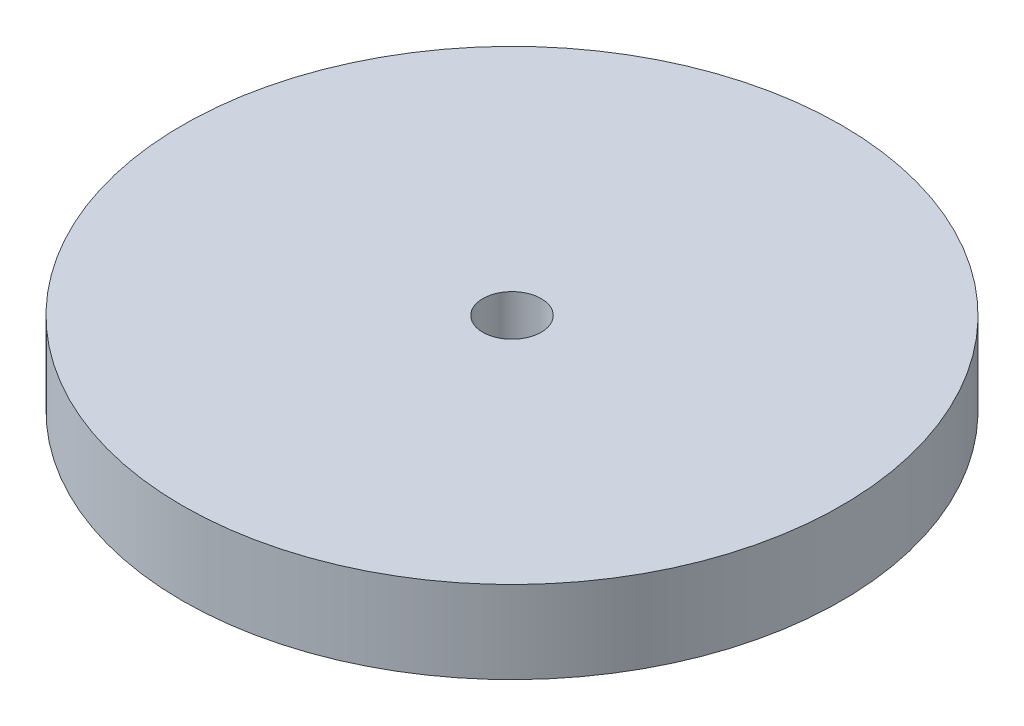
SolidWorks part; units mm, degrees
ref_plane "Front Plane" through (0, 0, 0) normal (0, 0, 1) x (1, 0, 0)
ref_plane "Top Plane" through (0, 0, 0) normal (0, 1, 0) x (1, 0, 0)
ref_plane "Right Plane" through (0, 0, 0) normal (1, 0, 0) x (0, 0, -1)
sketch "Sketch1" plane through (0, 0, 0) normal (0, 1, 0) x (1, 0, 0)
  circle A0 centre (0, 0) radius 12.7
  circle A1 centre (0, 0) radius 1.125
  dimension "D1" = 25.4
  dimension "D2" = 2.25
extrude "Boss-Extrude1" add sketch "Sketch1" against normal blind 3.175
